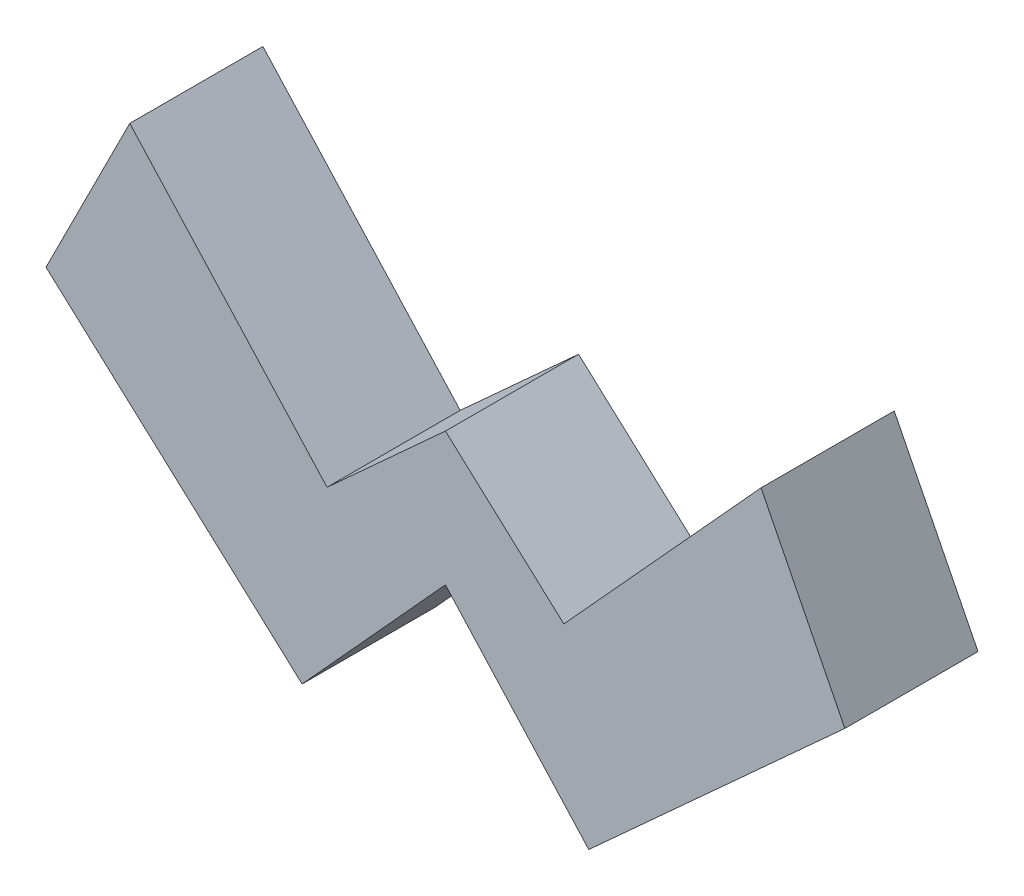
SolidWorks part; units mm, degrees
ref_plane "Front Plane" through (0, 0, 0) normal (0, 0, 1) x (1, 0, 0)
ref_plane "Top Plane" through (0, 0, 0) normal (0, 1, 0) x (1, 0, 0)
ref_plane "Right Plane" through (0, 0, 0) normal (1, 0, 0) x (0, 0, -1)
sketch "Sketch2" plane through (0, 0, 0) normal (0, 0, 1) x (1, 0, 0)
  line L0 (0, 0) -> (0, 5)
  line L1 (0, 5) -> (-4.4465, 0.9497)
  line L2 (-4.4465, 0.9497) -> (-11.854, 9.0816)
  line L3 (-11.854, 9.0816) -> (-15, 2.8284)
  line L4 (-15, 2.8284) -> (-5.3826, -5.9184)
  line L5 (-5.3826, -5.9184) -> (0, 0)
  line L6 (5.3826, -5.9184) -> (0, 0)
  line L7 (15, 2.8284) -> (5.3826, -5.9184)
  line L8 (11.854, 9.0816) -> (15, 2.8284)
  line L9 (4.4465, 0.9497) -> (11.854, 9.0816)
  line L10 (0, 5) -> (4.4465, 0.9497)
  dimension "D1" = 15
  dimension "D2" = 15
  dimension "D3" = 90
  dimension "D4" = 90
  dimension "D5" = 7
  dimension "D6" = 13
  dimension "D7" = 5
  dimension "D8" = 11
  dimension "D9" = 8
extrude "Boss-Extrude1" add sketch "Sketch2" along normal blind 5 contours L10 L0 L6 L7 L8 L9 | L4 L5 L0 L1 L2 L3
